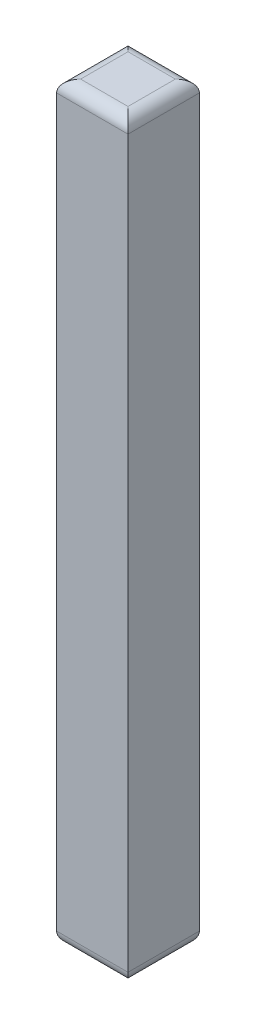
SolidWorks part; units mm, degrees
ref_plane "Front Plane" through (0, 0, 0) normal (0, 0, 1) x (1, 0, 0)
ref_plane "Top Plane" through (0, 0, 0) normal (0, 1, 0) x (1, 0, 0)
ref_plane "Right Plane" through (0, 0, 0) normal (1, 0, 0) x (0, 0, -1)
sketch "Sketch1" plane through (0, 0, 0) normal (0, 1, 0) x (1, 0, 0)
  line L1 (0, 0) -> (3.0226, 0)
  line L2 (0, 0) -> (0, 3.0226)
  line L3 (0, 3.0226) -> (3.0226, 3.0226)
  line L4 (3.0226, 0) -> (3.0226, 3.0226)
  dimension "D1" = 3.0226
  dimension "D2" = 3.0226
extrude "Boss-Extrude1" add sketch "Sketch1" along normal blind 31.75
fillet "Fillet1" radius 0.508 8 edges at (1.5113, 31.75, -3.0226) (3.0226, 31.75, -1.5113) (1.5113, 31.75, 0) (0, 31.75, -1.5113) (1.5113, 0, 0) (3.0226, 0, -1.5113) (1.5113, 0, -3.0226) (0, 0, -1.5113)
